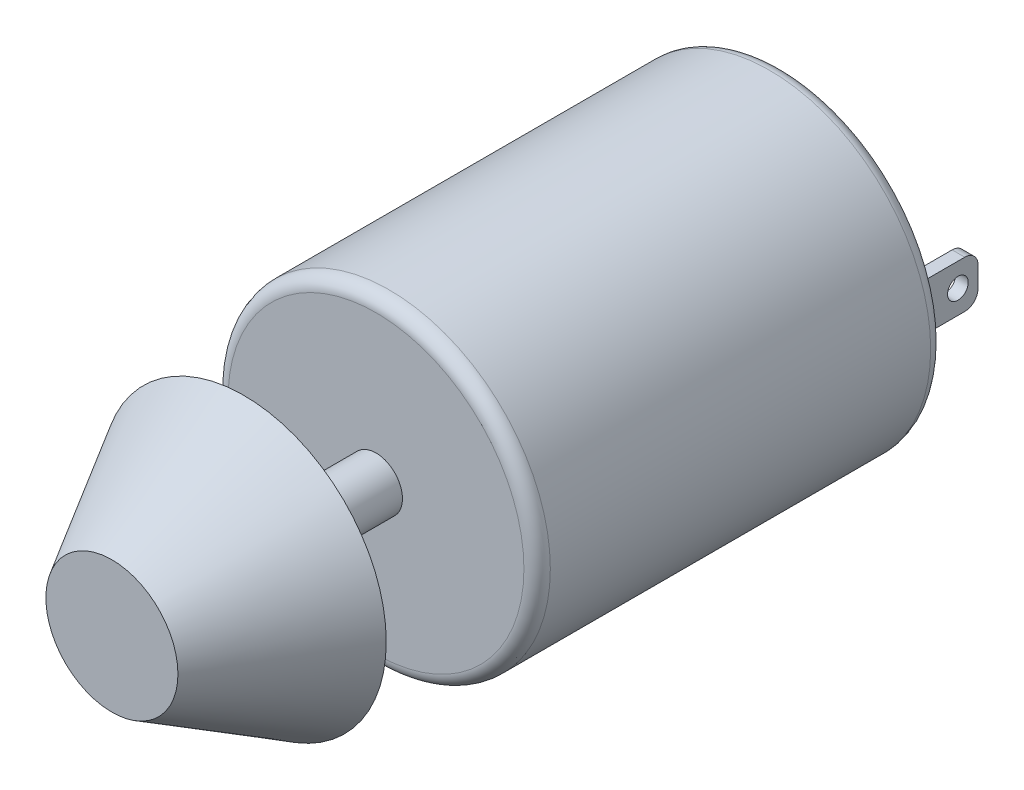
SolidWorks part; units mm, degrees
material "201.0-T43 Molde de fundição com isolamento (SS)"
ref_plane "Plano frontal" through (0, 0, 0) normal (0, 0, 1) x (1, 0, 0)
ref_plane "Plano superior" through (0, 0, 0) normal (0, 1, 0) x (1, 0, 0)
ref_plane "Plano direito" through (0, 0, 0) normal (1, 0, 0) x (0, 0, -1)
sketch "Esboço1" plane through (0, 0, 0) normal (0, 0, 1) x (1, 0, 0)
  circle A0 centre (0, 0) radius 12.2
  dimension "D1" = 24.4
extrude "Ressalto-extrusão1" add sketch "Esboço1" along normal blind 30.8
fillet "Filete1" radius 1 2 edges at (12.2, 0, 0) (12.2, 0, 30.8)
sketch "Esboço2" plane through (0, 0, 30.8) normal (0, 0, 1) x (1, 0, 0)
  circle A0 centre (0, 0) radius 2
  dimension "D1" = 4
extrude "Ressalto-extrusão2" add sketch "Esboço2" along normal blind 10
sketch "Esboço4" plane through (0, 0, 0) normal (0, 0, -1) x (-1, 0, 0)
  line L1 (-9.7828, 2.3302) -> (-8.8239, 2.3302)
  line L2 (-9.7828, 2.3302) -> (-9.7828, -1.234)
  line L3 (-9.7828, -1.234) -> (-8.8239, -1.234)
  line L4 (-8.8239, 2.3302) -> (-8.8239, -1.234)
  line L5 (8.817, 2.3302) -> (7.9226, 2.3302)
  line L6 (8.817, 2.3302) -> (8.817, -1.234)
  line L7 (8.817, -1.234) -> (7.9226, -1.234)
  line L8 (7.9226, 2.3302) -> (7.9226, -1.234)
extrude "Ressalto-extrusão3" add sketch "Esboço4" along normal blind 5
fillet "Filete2" radius 1 4 edges at (-8.3698, 2.3302, -5) (-8.3698, -1.234, -5) (9.3034, 2.3302, -5) (9.3034, -1.234, -5)
sketch "Esboço5" plane through (9.7828, 0, 0) normal (1, 0, 0) x (0, 0, -1)
  circle A0 centre (3.4772, 0.5481) radius 0.7821
extrude "Corte-extrusão2" cut sketch "Esboço5" against normal through all
sketch "Esboço6" plane through (0, 0, 40.8) normal (0, 0, 1) x (1, 0, 0)
  circle A0 centre (0, 0) radius 5
  dimension "D1" = 10
extrude "Ressalto-extrusão5" add sketch "Esboço6" along normal blind 10
draft "Inclinação3" type of draft neutral plane draft angle 30 faces to draft 1 face at (5, 0, 50.8) neutral plane through (0, 0, 50.8) neutral plane normal (0, 0, 1) parameters "D1"=30
